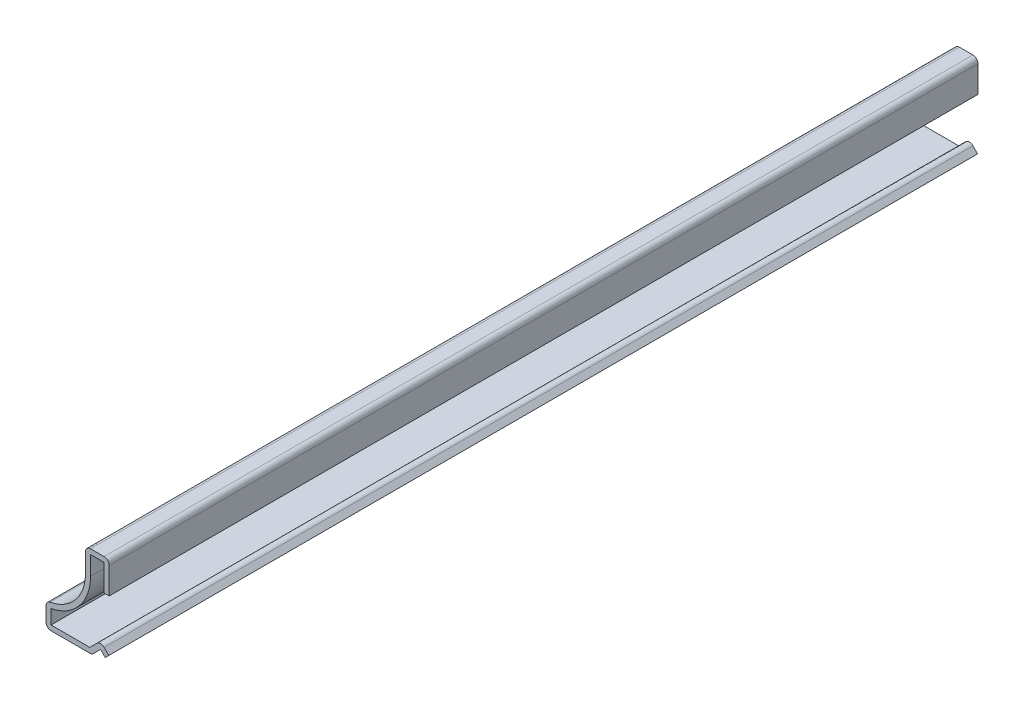
SolidWorks part; units mm, degrees
ref_plane "Front Plane" through (0, 0, 0) normal (0, 0, 1) x (1, 0, 0)
ref_plane "Top Plane" through (0, 0, 0) normal (0, 1, 0) x (1, 0, 0)
ref_plane "Right Plane" through (0, 0, 0) normal (1, 0, 0) x (0, 0, -1)
sketch "Sketch1" plane through (0, 0, 0) normal (0, 0, 1) x (1, 0, 0)
  line L0 (0, 11.9062) -> (0, 18.2562)
  line L1 (0, 18.2562) -> (-4.7625, 18.2563)
  line L2 (-4.7625, 18.2563) -> (-4.7625, 13.4576)
  line L3 (-12.7, 4.7625) -> (-12.7, 0)
  line L4 (-12.7, 0) -> (-3.4763, 0)
  line L5 (-3.4763, 0) -> (-1.7382, 1.7382)
  line L6 (-1.7382, 1.7382) -> (-0.7937, 0.7938)
  line L7 (-1.016, 11.9062) -> (-1.016, 17.2402)
  line L8 (-1.016, 17.2402) -> (-3.7465, 17.2402)
  line L9 (-3.7465, 17.2402) -> (-3.7465, 13.4576)
  line L10 (-11.684, 3.8798) -> (-11.684, 1.016)
  line L11 (-11.684, 1.016) -> (-3.8972, 1.016)
  line L12 (-3.8972, 1.016) -> (-1.7382, 3.175)
  line L13 (-1.7382, 3.175) -> (-0.0753, 1.5122)
  line L14 (0, 11.9062) -> (-1.016, 11.9062)
  line L15 (-0.7937, 0.7938) -> (-0.0753, 1.5122)
  arc A0 (-4.7625, 13.4576) -> (-12.7, 4.7625) centre (-13.4938, 13.4576) cw
  arc A1 (-3.7465, 13.4576) -> (-11.684, 3.8798) centre (-13.4938, 13.4576) cw
  point P7 (-0.4509, 1.3245)
  point P12 (0, 0)
  point P13 (-13.4937, 13.4421)
  point P14 (-13.4937, 13.3857)
  point P15 (-0.298, 1.2623)
  point P16 (-6.4065, 0)
  point P17 (0, 0)
  point P18 (-6.3514, 0)
  point P31 (-3.0166, 4.4534)
  dimension "D2" = 8.7312
  dimension "D1" = 4.7625
  dimension "D3" = 4.7625
  dimension "D4" = 6.35
  dimension "D5" = 7.9375
  dimension "D6" = 13.4937
  dimension "D7" = 0.7937
  dimension "D8" = 3.175
  dimension "D9" = 11.9062
  dimension "D10" = 45
  dimension "D11" = 1.016
extrude "Boss-Extrude1" add sketch "Sketch1" against normal blind 174.625
fillet "Fillet1" radius 1.016 6 edges at (-1.7382, 3.175, -87.3125) (-3.4763, 0, -87.3125) (-12.7, 0, -87.3125) (-12.7, 4.7625, -87.3125) (-4.7625, 18.2563, -87.3125) (0, 18.2562, -87.3125)
